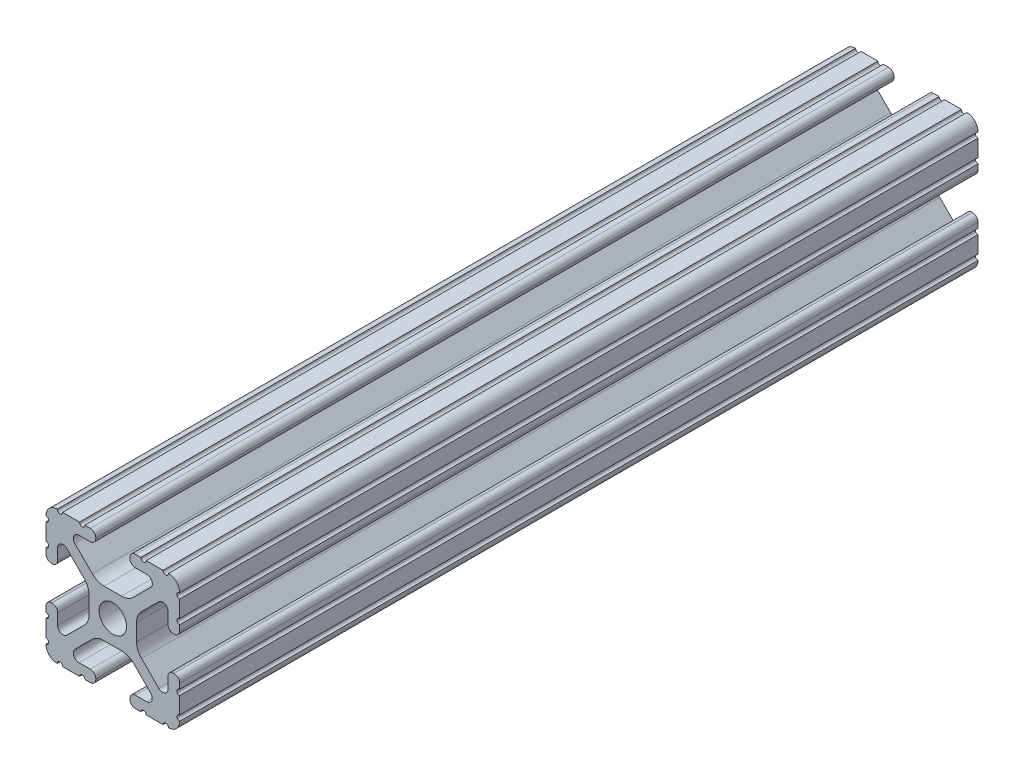
SolidWorks part; units mm, degrees
ref_plane "Front Plane" through (0, 0, 0) normal (0, 0, 1) x (1, 0, 0)
ref_plane "Top Plane" through (0, 0, 0) normal (0, 1, 0) x (1, 0, 0)
ref_plane "Right Plane" through (0, 0, 0) normal (1, 0, 0) x (0, 0, -1)
sketch "Sketch1" plane through (0, 0, 0) normal (0, 0, 1) x (1, 0, 0)
  line L88 (-7.1797, -8.6452) -> (-3.9523, -5.4237)
  line L89 (-1.7093, -4.4958) -> (1.7093, -4.4958)
  line L90 (3.9523, -5.4237) -> (7.1797, -8.6452)
  line L91 (6.4164, -10.4902) -> (4.2875, -10.4902)
  line L92 (3.2385, -11.5392) -> (3.2385, -11.651)
  line L93 (4.2875, -12.7) -> (5.3171, -12.7)
  line L94 (6.3331, -12.7) -> (9.5504, -12.7)
  line L95 (12.7, -9.5504) -> (12.7, -6.3331)
  line L96 (12.7, -5.3171) -> (12.7, -4.2875)
  line L97 (11.651, -3.2385) -> (11.5392, -3.2385)
  line L98 (10.4902, -4.2875) -> (10.4902, -6.4021)
  line L99 (8.7371, -7.1294) -> (5.441, -3.8408)
  line L100 (4.5085, -1.5932) -> (4.5085, 1.5932)
  line L101 (5.441, 3.8408) -> (8.7371, 7.1294)
  line L102 (10.4902, 6.4021) -> (10.4902, 4.2875)
  line L103 (11.5392, 3.2385) -> (11.651, 3.2385)
  line L104 (12.7, 4.2875) -> (12.7, 5.3171)
  line L105 (12.7, 6.3331) -> (12.7, 9.5504)
  line L106 (9.5504, 12.7) -> (6.3331, 12.7)
  line L107 (5.3171, 12.7) -> (4.2875, 12.7)
  line L108 (3.2385, 11.651) -> (3.2385, 11.5392)
  line L109 (4.2875, 10.4902) -> (6.4768, 10.4902)
  line L110 (7.207, 8.7244) -> (3.8983, 5.4232)
  line L111 (1.6558, 4.4958) -> (-1.6558, 4.4958)
  line L112 (-3.8983, 5.4232) -> (-7.207, 8.7244)
  line L113 (-6.4768, 10.4902) -> (-4.2875, 10.4902)
  line L114 (-3.2385, 11.5392) -> (-3.2385, 11.651)
  line L115 (-4.2875, 12.7) -> (-5.3171, 12.7)
  line L116 (-6.3331, 12.7) -> (-9.5504, 12.7)
  line L117 (-12.7, 9.5504) -> (-12.7, 6.3331)
  line L118 (-12.7, 5.3171) -> (-12.7, 4.2875)
  line L119 (-11.651, 3.2385) -> (-11.5392, 3.2385)
  line L120 (-10.4902, 4.2875) -> (-10.4902, 6.4021)
  line L121 (-8.7371, 7.1294) -> (-5.441, 3.8408)
  line L122 (-4.5085, 1.5932) -> (-4.5085, -1.5932)
  line L123 (-5.441, -3.8408) -> (-8.7371, -7.1294)
  line L124 (-10.4902, -6.4021) -> (-10.4902, -4.2875)
  line L125 (-11.5392, -3.2385) -> (-11.651, -3.2385)
  line L126 (-12.7, -4.2875) -> (-12.7, -5.3171)
  line L127 (-12.7, -6.3331) -> (-12.7, -9.5504)
  line L128 (-9.5504, -12.7) -> (-6.3331, -12.7)
  line L129 (-5.3171, -12.7) -> (-4.2875, -12.7)
  line L130 (-3.2385, -11.651) -> (-3.2385, -11.5392)
  line L131 (-4.2875, -10.4902) -> (-6.4164, -10.4902)
  circle A1 centre (0, 0) radius 2.6035
  arc A104 (-7.1797, -8.6452) -> (-6.4164, -10.4902) centre (-6.4164, -9.4098) ccw
  arc A105 (-1.7093, -4.4958) -> (-3.9523, -5.4237) centre (-1.7093, -7.6708) ccw
  arc A106 (3.9523, -5.4237) -> (1.7093, -4.4958) centre (1.7093, -7.6708) ccw
  arc A107 (6.4164, -10.4902) -> (7.1797, -8.6452) centre (6.4164, -9.4098) ccw
  arc A108 (4.2875, -10.4902) -> (3.2385, -11.5392) centre (4.2875, -11.5392) ccw
  arc A109 (3.2385, -11.651) -> (4.2875, -12.7) centre (4.2875, -11.651) ccw
  arc A110 (6.3331, -12.7) -> (5.3171, -12.7) centre (5.8251, -12.7) ccw
  arc A111 (10.5664, -12.6998) -> (9.5504, -12.7) centre (10.0584, -12.7) ccw
  arc A112 (10.5664, -12.6998) -> (12.6998, -10.5664) centre (10.5918, -10.5918) ccw
  arc A113 (12.7, -9.5504) -> (12.6998, -10.5664) centre (12.7, -10.0584) ccw
  arc A114 (12.7, -5.3171) -> (12.7, -6.3331) centre (12.7, -5.8251) ccw
  arc A115 (12.7, -4.2875) -> (11.651, -3.2385) centre (11.651, -4.2875) ccw
  arc A116 (11.5392, -3.2385) -> (10.4902, -4.2875) centre (11.5392, -4.2875) ccw
  arc A117 (8.7371, -7.1294) -> (10.4902, -6.4021) centre (9.4628, -6.4021) ccw
  arc A118 (4.5085, -1.5932) -> (5.441, -3.8408) centre (7.6835, -1.5932) ccw
  arc A119 (5.441, 3.8408) -> (4.5085, 1.5932) centre (7.6835, 1.5932) ccw
  arc A120 (10.4902, 6.4021) -> (8.7371, 7.1294) centre (9.4628, 6.4021) ccw
  arc A121 (10.4902, 4.2875) -> (11.5392, 3.2385) centre (11.5392, 4.2875) ccw
  arc A122 (11.651, 3.2385) -> (12.7, 4.2875) centre (11.651, 4.2875) ccw
  arc A123 (12.7, 6.3331) -> (12.7, 5.3171) centre (12.7, 5.8251) ccw
  arc A124 (12.6998, 10.5664) -> (12.7, 9.5504) centre (12.7, 10.0584) ccw
  arc A125 (12.6998, 10.5664) -> (10.5664, 12.6998) centre (10.5918, 10.5918) ccw
  arc A126 (9.5504, 12.7) -> (10.5664, 12.6998) centre (10.0584, 12.7) ccw
  arc A127 (5.3171, 12.7) -> (6.3331, 12.7) centre (5.8251, 12.7) ccw
  arc A128 (4.2875, 12.7) -> (3.2385, 11.651) centre (4.2875, 11.651) ccw
  arc A129 (3.2385, 11.5392) -> (4.2875, 10.4902) centre (4.2875, 11.5392) ccw
  arc A130 (7.207, 8.7244) -> (6.4768, 10.4902) centre (6.4768, 9.4563) ccw
  arc A131 (1.6558, 4.4958) -> (3.8983, 5.4232) centre (1.6558, 7.6708) ccw
  arc A132 (-3.8983, 5.4232) -> (-1.6558, 4.4958) centre (-1.6558, 7.6708) ccw
  arc A133 (-6.4768, 10.4902) -> (-7.207, 8.7244) centre (-6.4768, 9.4563) ccw
  arc A134 (-4.2875, 10.4902) -> (-3.2385, 11.5392) centre (-4.2875, 11.5392) ccw
  arc A135 (-3.2385, 11.651) -> (-4.2875, 12.7) centre (-4.2875, 11.651) ccw
  arc A136 (-6.3331, 12.7) -> (-5.3171, 12.7) centre (-5.8251, 12.7) ccw
  arc A137 (-10.5664, 12.6998) -> (-9.5504, 12.7) centre (-10.0584, 12.7) ccw
  arc A138 (-10.5664, 12.6998) -> (-12.6998, 10.5664) centre (-10.5918, 10.5918) ccw
  arc A139 (-12.7, 9.5504) -> (-12.6998, 10.5664) centre (-12.7, 10.0584) ccw
  arc A140 (-12.7, 5.3171) -> (-12.7, 6.3331) centre (-12.7, 5.8251) ccw
  arc A141 (-12.7, 4.2875) -> (-11.651, 3.2385) centre (-11.651, 4.2875) ccw
  arc A142 (-11.5392, 3.2385) -> (-10.4902, 4.2875) centre (-11.5392, 4.2875) ccw
  arc A143 (-8.7371, 7.1294) -> (-10.4902, 6.4021) centre (-9.4628, 6.4021) ccw
  arc A144 (-4.5085, 1.5932) -> (-5.441, 3.8408) centre (-7.6835, 1.5932) ccw
  arc A145 (-5.441, -3.8408) -> (-4.5085, -1.5932) centre (-7.6835, -1.5932) ccw
  arc A146 (-10.4902, -6.4021) -> (-8.7371, -7.1294) centre (-9.4628, -6.4021) ccw
  arc A147 (-10.4902, -4.2875) -> (-11.5392, -3.2385) centre (-11.5392, -4.2875) ccw
  arc A148 (-11.651, -3.2385) -> (-12.7, -4.2875) centre (-11.651, -4.2875) ccw
  arc A149 (-12.7, -6.3331) -> (-12.7, -5.3171) centre (-12.7, -5.8251) ccw
  arc A150 (-12.6998, -10.5664) -> (-12.7, -9.5504) centre (-12.7, -10.0584) ccw
  arc A151 (-12.6998, -10.5664) -> (-10.5664, -12.6998) centre (-10.5918, -10.5918) ccw
  arc A152 (-9.5504, -12.7) -> (-10.5664, -12.6998) centre (-10.0584, -12.7) ccw
  arc A153 (-5.3171, -12.7) -> (-6.3331, -12.7) centre (-5.8251, -12.7) ccw
  arc A154 (-4.2875, -12.7) -> (-3.2385, -11.651) centre (-4.2875, -11.651) ccw
  arc A155 (-3.2385, -11.5392) -> (-4.2875, -10.4902) centre (-4.2875, -11.5392) ccw
extrude "Boss-Extrude1" add sketch "Sketch1" along normal mid plane 1828.8
sketch "Sketch2" plane through (12.7, 0, 0) normal (1, 0, 0) x (0, 0, -1)
  line L0 (-843.2745, -109.9441) -> (-843.2745, 28.4774) construction
  line L1 (-174.9218, -42.647) -> (-174.9218, 41.3341) construction
  line L2 (-326.6728, 16.7947) -> (-326.6728, -17.9661)
  line L3 (-326.6728, -17.9661) -> (-918.4573, -17.9661)
  line L4 (-918.4573, -17.9661) -> (-918.4573, 16.7947)
  line L5 (-918.4573, 16.7947) -> (-326.6728, 16.7947)
  line L6 (-174.9218, -17.9661) -> (-174.9218, 18.2032)
  line L7 (-174.9218, 18.2032) -> (925.0572, 18.2032)
  line L8 (925.0572, 18.2032) -> (925.0572, -17.9661)
  line L9 (925.0572, -17.9661) -> (-174.9218, -17.9661)
  circle A0 centre (-852.7591, -105.1) radius 10.65 construction
  arc A1 (-164.2718, -31.997) -> (-164.2718, -53.297) centre (-164.2718, -42.647) ccw construction
  point P16 (-842.1274, -104.4767)
extrude "Cut-Extrude1" cut sketch "Sketch2" against normal blind 27.432
